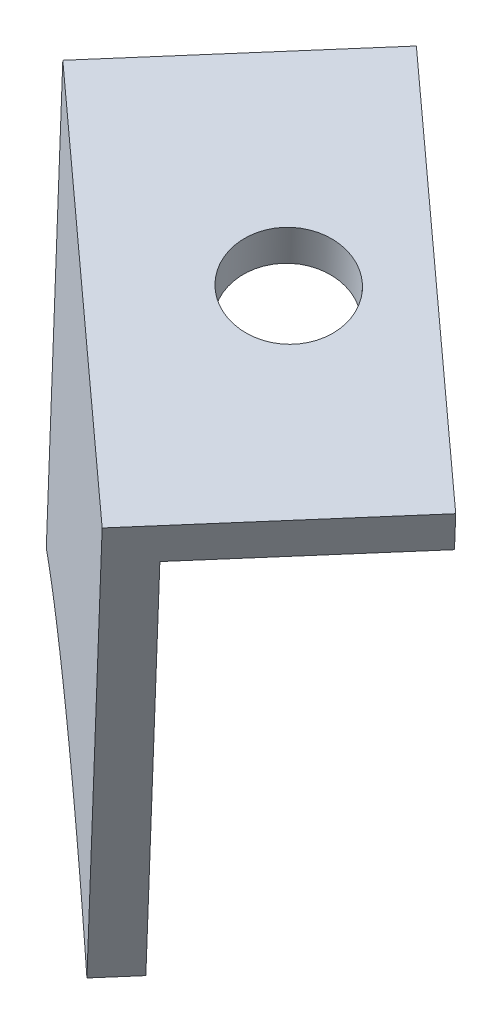
SolidWorks part; units mm, degrees
material "1.4105 (X6CrMoS17)"
ref_plane "Płaszczyzna XY" through (0, 0, 0) normal (0, 0, 1) x (1, 0, 0)
ref_plane "Płaszczyzna XZ" through (0, 0, 0) normal (0, 1, 0) x (1, 0, 0)
ref_plane "Płaszczyzna YZ" through (0, 0, 0) normal (1, 0, 0) x (0, 0, -1)
ref_plane "Płaszczyzna1" through (184.0502, 0, -211.7255) normal (0.6561, 0, -0.7547) x (-0.7547, 0, -0.6561)
sketch "Szkic1" plane through (184.0502, 0, -211.7255) normal (0.6561, 0, -0.7547) x (-0.7547, 0, -0.6561)
  line L2 (-818.7567, -341.5471) -> (-826.1543, -317.6667)
  line L3 (-799.0322, -337.6307) -> (-807.05, -311.7485)
  line L5 (-807.05, -311.7485) -> (-826.1543, -317.6667)
  spline S0 degree 3 poles (-826.726, -355.7471) (-833.6518, -331.7256) (-796.2995, -320.9562) (-789.3737, -344.9777) (-782.4478, -368.9992) (-819.8001, -379.7686) (-826.726, -355.7471) (-833.6518, -331.7256) (-796.2995, -320.9562) knots -0.5 0 0 0 0.5 0.5 0.5 1 1 1 1.5 1.5 1.5 weights 1 0.333333 0.333333 1 0.333333 0.333333 1 0.333333 0.333333 only from (-826.726, -355.7471) to (-826.726, -355.7471)
  spline S1 degree 3 poles (-818.7567, -341.5471) (-812.6515, -337.7435) (-805.3627, -336.3659) (-799.0322, -337.6307) knots 0.197302 0.197302 0.197302 0.197302 0.338155 0.338155 0.338155 0.338155 weights 0.522216 0.482629 0.495947 0.562171
  dimension "D1" = 90
  dimension "D2" = 311.7485
  dimension "D3" = 20
  dimension "D4" = 885.1232
  dimension "D6" = 25
extrude "Dodanie-wyciągnięcie1" add sketch "Szkic1" along normal blind 2 contours L3 L5 L2 S1
ref_plane "Płaszczyzna2" through (185.3623, 0, -213.2349) normal (0.6561, 0, -0.7547) x (-0.7547, 0, -0.6561)
sketch "Szkic2" plane through (185.3623, 0, -213.2349) normal (0.6561, 0, -0.7547) x (-0.7547, 0, -0.6561)
  line L0 (-826.1543, -317.6667) -> (-807.05, -311.7485)
extrude "Wyciągnięcie-cienka ścianka1" add sketch "Szkic2" along normal blind 10 thin
ref_plane "Płaszczyzna5" through (-13.6172, -58.2445, -11.8373) normal (-0.2233, -0.9552, -0.1941) x (-0.9747, 0.2189, 0.0445)
sketch "Szkic3" plane through (-13.6172, -58.2445, -11.8373) normal (-0.2233, -0.9552, -0.1941) x (-0.9747, 0.2189, 0.0445)
  line L0 (-835.2774, -364.595) -> (-828.5469, -371.9909) construction
  line L1 (-850.0692, -378.0561) -> (-835.2774, -364.595) construction
  circle A0 centre (-839.308, -375.0235) radius 2.5
  dimension "D1" = 5
  dimension "D2" = 10
  dimension "D3" = 5
extrude "Wytnij-wyciągnięcie1" cut sketch "Szkic3" against normal blind 6
